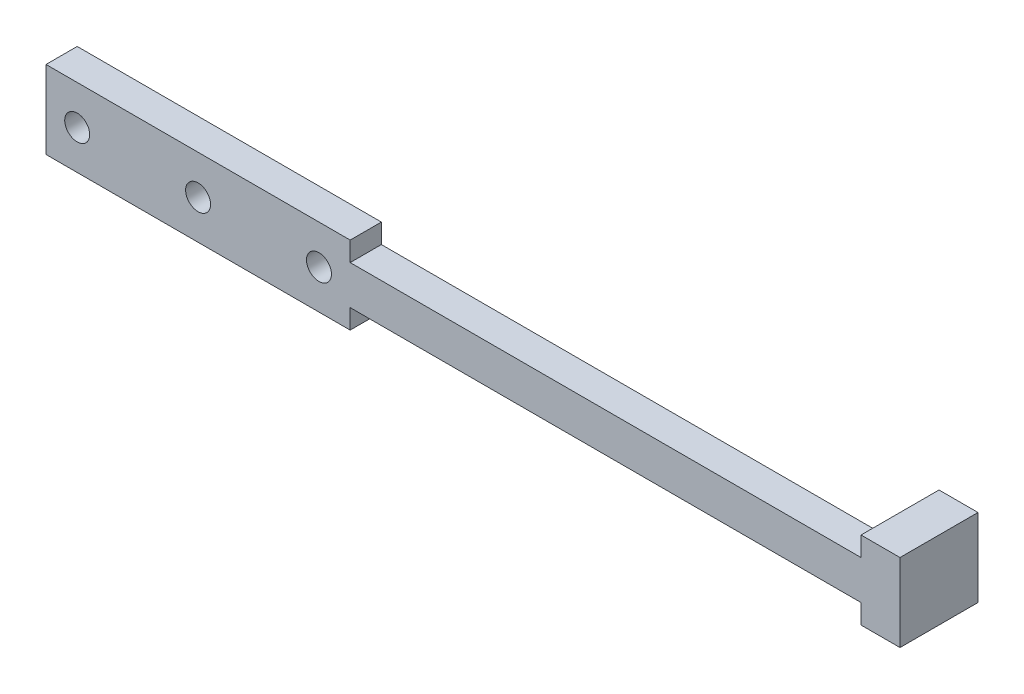
SolidWorks part; units mm, degrees
ref_plane "Plano frontal" through (0, 0, 0) normal (0, 0, 1) x (1, 0, 0)
ref_plane "Plano superior" through (0, 0, 0) normal (0, 1, 0) x (1, 0, 0)
ref_plane "Plano direito" through (0, 0, 0) normal (1, 0, 0) x (0, 0, -1)
sketch "Esboço1" plane through (0, 0, 0) normal (0, 0, 1) x (1, 0, 0)
  line L0 (-32.75, 5) -> (-32.75, 2.5)
  line L1 (-32.75, 2.5) -> (32.75, 2.5)
  line L2 (-32.75, 2.5) -> (-32.75, -2.5)
  line L3 (-32.75, -2.5) -> (32.75, -2.5)
  line L4 (32.75, 2.5) -> (32.75, -2.5)
  line L5 (-32.75, 2.5) -> (32.75, -2.5) construction
  line L6 (-32.75, -2.5) -> (32.75, 2.5) construction
  line L7 (-71.75, 5) -> (-32.75, 5)
  line L8 (-71.75, 5) -> (-71.75, -5)
  line L9 (-71.75, -5) -> (-32.75, -5)
  line L10 (-32.75, 5) -> (-32.75, -5) construction
  line L11 (-71.75, 5) -> (-32.75, -5) construction
  line L12 (-71.75, -5) -> (-32.75, 5) construction
  line L13 (-32.75, -2.5) -> (-32.75, -5)
  line L14 (-52.25, 0) -> (-52.25, -4.4736) construction
  circle A0 centre (-36.75, 0) radius 1.6
  circle A1 centre (-67.75, 0) radius 1.6
  circle A2 centre (-52.25, 0) radius 1.6
  point P0 (0, 0)
  point P6 (-52.25, 0)
  point P19 (0, 0)
  point P20 (-20.1902, 0)
  point P21 (-20.6446, 0)
  point P22 (0, 0)
  point P23 (-35.597, 0.1404)
  dimension "D3" = 3.2
  dimension "D1" = 5
  dimension "D2" = 85
  dimension "D4" = 10
  dimension "D5" = 31
  dimension "D6" = 4
extrude "Ressalto-extrusão1" add sketch "Esboço1" along normal blind 4 contours L13 L2 L0 L7 L8 L9 A2 A1 A0 | L4 L1 L2 L3
sketch "Esboço2" plane through (0, 0, 4) normal (0, 0, 1) x (1, 0, 0)
  line L0 (32.75, 2.5) -> (32.75, -2.5) construction
  line L1 (32.75, 5) -> (37.75, 5)
  line L2 (32.75, 5) -> (32.75, -5)
  line L3 (32.75, -5) -> (37.75, -5)
  line L4 (37.75, 5) -> (37.75, -5)
  point P8 (32.75, 0)
  point P9 (32.75, 0)
  dimension "D1" = 5
  dimension "D2" = 10
extrude "Ressalto-extrusão2" add sketch "Esboço2" against normal blind 10
